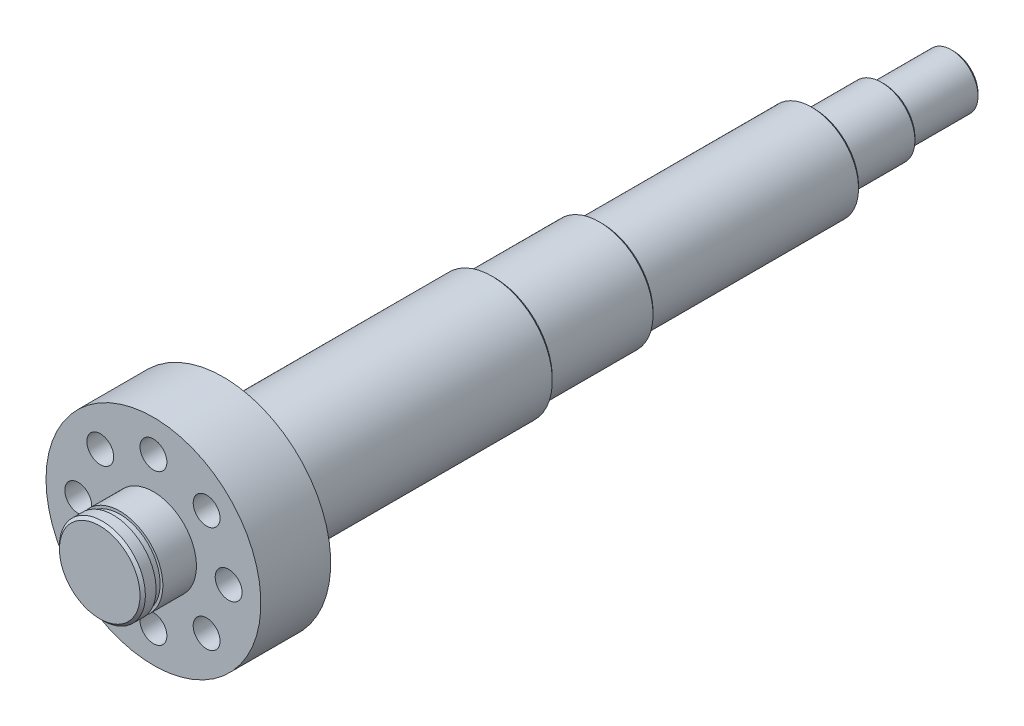
SolidWorks part; units mm, degrees
ref_plane "前视基准面" through (0, 0, 0) normal (0, 0, 1) x (1, 0, 0)
ref_plane "上视基准面" through (0, 0, 0) normal (0, 1, 0) x (1, 0, 0)
ref_plane "右视基准面" through (0, 0, 0) normal (1, 0, 0) x (0, 0, -1)
sketch "草图1" plane through (0, 0, 0) normal (0, 0, 1) x (1, 0, 0)
  circle A0 centre (0, 0) radius 16
  dimension "D1" = 32
extrude "凸台-拉伸1" add sketch "草图1" along normal blind 20
sketch "草图2" plane through (0, 0, 0) normal (0, 0, -1) x (-1, 0, 0)
  circle A0 centre (0, 0) radius 40
  dimension "D1" = 80
extrude "凸台-拉伸2" add sketch "草图2" along normal blind 26
sketch "草图3" plane through (0, 0, 0) normal (0, 1, 0) x (1, 0, 0)
  line L0 (16, -20) -> (16, 0) construction
  line L1 (16, -12.5) -> (15, -12.5)
  line L2 (16, -12.5) -> (16, -15)
  line L3 (16, -15) -> (15, -15)
  line L4 (15, -12.5) -> (15, -15)
  line L5 (-16, -20) -> (16, -20) construction
  line L6 (0, 0) -> (0, -23.2144) construction
  dimension "D1" = 1
  dimension "D2" = 2.5
  dimension "D3" = 5
revolve "切除-旋转1" cut sketch "草图3" angle 360 about L6
sketch "草图4" plane through (0, 0, 0) normal (0, 0, 1) x (1, 0, 0)
  circle A0 centre (28, 0) radius 5
  dimension "D1" = 10
  dimension "D2" = 28
extrude "切除-拉伸1" cut sketch "草图4" against normal blind 8
pattern_circular "阵列(圆周)1" count 8 over 360 about axis through (0, 0, 0) along (0, 0, 1) of "切除-拉伸1"
chamfer "倒角1" distance 1 angle 45 1 edges at (16, 0, 20)
sketch "草图5" plane through (0, 0, -26) normal (0, 0, -1) x (-1, 0, 0)
  circle A0 centre (0, 0) radius 22.5
  dimension "D1" = 45
extrude "凸台-拉伸3" add sketch "草图5" along normal blind 101
sketch "草图6" plane through (0, 0, -127) normal (0, 0, -1) x (-1, 0, 0)
  circle A0 centre (0, 0) radius 20
  dimension "D1" = 40
extrude "凸台-拉伸4" add sketch "草图6" along normal blind 40
cosmetic thread "装饰螺纹线1" parameters "D2"=35.752
sketch "草图7" plane through (0, 0, -167) normal (0, 0, -1) x (-1, 0, 0)
  circle A0 centre (0, 0) radius 17.5
  dimension "D1" = 35
extrude "凸台-拉伸5" add sketch "草图7" along normal blind 79
sketch "草图8" plane through (0, 0, -246) normal (0, 0, -1) x (-1, 0, 0)
  circle A0 centre (0, 0) radius 12.5
  dimension "D1" = 25
extrude "凸台-拉伸6" add sketch "草图8" along normal blind 26
sketch "草图9" plane through (0, 0, -272) normal (0, 0, -1) x (-1, 0, 0)
  circle A0 centre (0, 0) radius 10
  dimension "D1" = 20
extrude "凸台-拉伸7" add sketch "草图9" along normal blind 26
chamfer "倒角2" distance 1 angle 45 4 edges at (-10, 0, -298) (-12.5, 0, -272) (-17.5, 0, -246) (-20, 0, -167)
chamfer "倒角3" distance 1 angle 45 1 edges at (-22.5, 0, -127)
sketch "草图10" plane through (0, 0, -298) normal (0, 0, -1) x (-1, 0, 0)
  circle A0 centre (-6, 0.2413) radius 2.5
  circle A1 centre (6, 0) radius 2.5
  dimension "D1" = 5
  dimension "D2" = 5
  dimension "D3" = 12
  dimension "D4" = 6
extrude "切除-拉伸2" cut sketch "草图10" against normal blind 7
